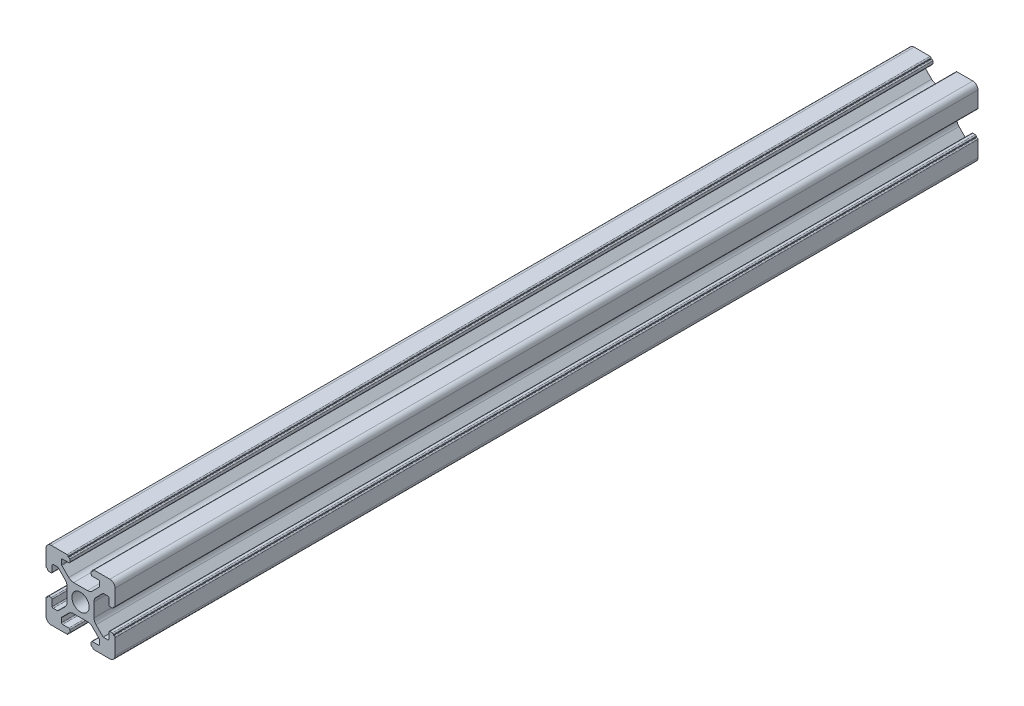
SolidWorks part; units mm, degrees
ref_plane "Front Plane" through (0, 0, 0) normal (0, 0, 1) x (1, 0, 0)
ref_plane "Top Plane" through (0, 0, 0) normal (0, 1, 0) x (1, 0, 0)
ref_plane "Right Plane" through (0, 0, 0) normal (1, 0, 0) x (0, 0, -1)
sketch "Model" plane through (0, 0, 0) normal (0, 0, 1) x (1, 0, 0)
  line L0 (7.8, 0) -> (7.8, -4.0218)
  line L1 (8.9716, -6.8503) -> (13.1213, -11)
  line L2 (13.1213, -11) -> (15.8, -11)
  line L3 (16.4, -10.4) -> (16.4, -6.8)
  line L4 (17, -6.2) -> (18.4, -6.2)
  line L5 (19, -6.8) -> (19, -7.2)
  line L6 (19, -7.2) -> (19.4, -7.2)
  line L7 (20, -7.8) -> (20, -17)
  line L8 (17, -20) -> (7.8, -20)
  line L9 (6.2, -18.4) -> (6.2, -17)
  line L10 (6.8, -16.4) -> (10.4, -16.4)
  line L11 (11, -15.8) -> (11, -13.3698)
  line L12 (10.8243, -12.9456) -> (6.8503, -8.9716)
  line L13 (4.0218, -7.8) -> (0, -7.8)
  line L14 (0, -7.8) -> (-4.0218, -7.8)
  line L15 (-6.8503, -8.9716) -> (-10.8243, -12.9456)
  line L16 (-11, -13.3698) -> (-11, -15.8)
  line L17 (-10.4, -16.4) -> (-6.8, -16.4)
  line L18 (-6.2, -17) -> (-6.2, -18.4)
  line L19 (-7.8, -20) -> (-17, -20)
  line L20 (-20, -17) -> (-20, -7.8)
  line L21 (-19.4, -7.2) -> (-19, -7.2)
  line L22 (-19, -7.2) -> (-19, -6.8)
  line L23 (-18.4, -6.2) -> (-17, -6.2)
  line L24 (-16.4, -6.8) -> (-16.4, -10.4)
  line L25 (-15.8, -11) -> (-13.3698, -11)
  line L26 (-12.9456, -10.8243) -> (-8.9716, -6.8503)
  line L27 (-7.8, -4.0218) -> (-7.8, 0)
  line L28 (-7.8, 0) -> (-7.8, 4.0218)
  line L29 (-8.9716, 6.8503) -> (-12.9456, 10.8243)
  line L30 (-13.3698, 11) -> (-15.8, 11)
  line L31 (-16.4, 10.4) -> (-16.4, 6.8)
  line L32 (-17, 6.2) -> (-18.4, 6.2)
  line L33 (-19, 6.8) -> (-19, 7.2)
  line L34 (-19, 7.2) -> (-19.4, 7.2)
  line L35 (-20, 7.8) -> (-20, 17)
  line L36 (-17, 20) -> (-7.8, 20)
  line L37 (-7.2, 19.4) -> (-7.2, 19)
  line L38 (-7.2, 19) -> (-6.8, 19)
  line L39 (-6.2, 18.4) -> (-6.2, 17)
  line L40 (-6.8, 16.4) -> (-10.4, 16.4)
  line L41 (-11, 15.8) -> (-11, 13.3698)
  line L42 (-10.8243, 12.9456) -> (-6.8503, 8.9716)
  line L43 (-4.0218, 7.8) -> (0, 7.8)
  line L44 (0, 7.8) -> (4.0218, 7.8)
  line L45 (6.8503, 8.9716) -> (10.8243, 12.9456)
  line L46 (11, 13.3698) -> (11, 15.8)
  line L47 (10.4, 16.4) -> (6.8, 16.4)
  line L48 (6.2, 17) -> (6.2, 18.4)
  line L49 (6.8, 19) -> (7.2, 19)
  line L50 (7.2, 19) -> (7.2, 19.4)
  line L51 (7.8, 20) -> (17, 20)
  line L52 (20, 17) -> (20, 7.8)
  line L53 (19.4, 7.2) -> (19, 7.2)
  line L54 (19, 7.2) -> (19, 6.8)
  line L55 (18.4, 6.2) -> (17, 6.2)
  line L56 (16.4, 6.8) -> (16.4, 10.4)
  line L57 (15.8, 11) -> (13.3698, 11)
  line L58 (12.9456, 10.8243) -> (8.9716, 6.8503)
  line L59 (7.8, 4.0218) -> (7.8, 0)
  circle A0 centre (0, 0) radius 5
  arc A1 (7.8, -4.0218) -> (8.9716, -6.8503) centre (11.8, -4.0218) ccw
  arc A2 (15.8, -11) -> (16.4, -10.4) centre (15.8, -10.4) ccw
  arc A3 (17, -6.2) -> (16.4, -6.8) centre (17, -6.8) ccw
  arc A4 (19, -6.8) -> (18.4, -6.2) centre (18.4, -6.8) ccw
  arc A5 (20, -7.8) -> (19.4, -7.2) centre (19.4, -7.8) ccw
  arc A6 (17, -20) -> (20, -17) centre (17, -17) ccw
  arc A7 (7.2, -19.4) -> (7.8, -20) centre (7.8, -19.4) ccw
  arc A8 (7.2, -19.4) -> (6.8, -19) centre (6.8, -19.4) ccw
  arc A9 (6.2, -18.4) -> (6.8, -19) centre (6.8, -18.4) ccw
  arc A10 (6.8, -16.4) -> (6.2, -17) centre (6.8, -17) ccw
  arc A11 (10.4, -16.4) -> (11, -15.8) centre (10.4, -15.8) ccw
  arc A12 (11, -13.3698) -> (10.8243, -12.9456) centre (10.4, -13.3698) ccw
  arc A13 (6.8503, -8.9716) -> (4.0218, -7.8) centre (4.0218, -11.8) ccw
  arc A14 (-4.0218, -7.8) -> (-6.8503, -8.9716) centre (-4.0218, -11.8) ccw
  arc A15 (-10.8243, -12.9456) -> (-11, -13.3698) centre (-10.4, -13.3698) ccw
  arc A16 (-11, -15.8) -> (-10.4, -16.4) centre (-10.4, -15.8) ccw
  arc A17 (-6.2, -17) -> (-6.8, -16.4) centre (-6.8, -17) ccw
  arc A18 (-6.8, -19) -> (-6.2, -18.4) centre (-6.8, -18.4) ccw
  arc A19 (-6.8, -19) -> (-7.2, -19.4) centre (-6.8, -19.4) ccw
  arc A20 (-7.8, -20) -> (-7.2, -19.4) centre (-7.8, -19.4) ccw
  arc A21 (-20, -17) -> (-17, -20) centre (-17, -17) ccw
  arc A22 (-19.4, -7.2) -> (-20, -7.8) centre (-19.4, -7.8) ccw
  arc A23 (-18.4, -6.2) -> (-19, -6.8) centre (-18.4, -6.8) ccw
  arc A24 (-16.4, -6.8) -> (-17, -6.2) centre (-17, -6.8) ccw
  arc A25 (-16.4, -10.4) -> (-15.8, -11) centre (-15.8, -10.4) ccw
  arc A26 (-13.3698, -11) -> (-12.9456, -10.8243) centre (-13.3698, -10.4) ccw
  arc A27 (-8.9716, -6.8503) -> (-7.8, -4.0218) centre (-11.8, -4.0218) ccw
  arc A28 (-7.8, 4.0218) -> (-8.9716, 6.8503) centre (-11.8, 4.0218) ccw
  arc A29 (-12.9456, 10.8243) -> (-13.3698, 11) centre (-13.3698, 10.4) ccw
  arc A30 (-15.8, 11) -> (-16.4, 10.4) centre (-15.8, 10.4) ccw
  arc A31 (-17, 6.2) -> (-16.4, 6.8) centre (-17, 6.8) ccw
  arc A32 (-19, 6.8) -> (-18.4, 6.2) centre (-18.4, 6.8) ccw
  arc A33 (-20, 7.8) -> (-19.4, 7.2) centre (-19.4, 7.8) ccw
  arc A34 (-17, 20) -> (-20, 17) centre (-17, 17) ccw
  arc A35 (-7.2, 19.4) -> (-7.8, 20) centre (-7.8, 19.4) ccw
  arc A36 (-6.2, 18.4) -> (-6.8, 19) centre (-6.8, 18.4) ccw
  arc A37 (-6.8, 16.4) -> (-6.2, 17) centre (-6.8, 17) ccw
  arc A38 (-10.4, 16.4) -> (-11, 15.8) centre (-10.4, 15.8) ccw
  arc A39 (-11, 13.3698) -> (-10.8243, 12.9456) centre (-10.4, 13.3698) ccw
  arc A40 (-6.8503, 8.9716) -> (-4.0218, 7.8) centre (-4.0218, 11.8) ccw
  arc A41 (4.0218, 7.8) -> (6.8503, 8.9716) centre (4.0218, 11.8) ccw
  arc A42 (10.8243, 12.9456) -> (11, 13.3698) centre (10.4, 13.3698) ccw
  arc A43 (11, 15.8) -> (10.4, 16.4) centre (10.4, 15.8) ccw
  arc A44 (6.2, 17) -> (6.8, 16.4) centre (6.8, 17) ccw
  arc A45 (6.8, 19) -> (6.2, 18.4) centre (6.8, 18.4) ccw
  arc A46 (7.8, 20) -> (7.2, 19.4) centre (7.8, 19.4) ccw
  arc A47 (20, 17) -> (17, 20) centre (17, 17) ccw
  arc A48 (19.4, 7.2) -> (20, 7.8) centre (19.4, 7.8) ccw
  arc A49 (18.4, 6.2) -> (19, 6.8) centre (18.4, 6.8) ccw
  arc A50 (16.4, 6.8) -> (17, 6.2) centre (17, 6.8) ccw
  arc A51 (16.4, 10.4) -> (15.8, 11) centre (15.8, 10.4) ccw
  arc A52 (13.3698, 11) -> (12.9456, 10.8243) centre (13.3698, 10.4) ccw
  arc A53 (8.9716, 6.8503) -> (7.8, 4.0218) centre (11.8, 4.0218) ccw
extrude "Boss-Extrude1" add sketch "Model" along normal blind 500
scale "Scale1" bodies to scale 101 scale about centroid uniform scaling yes scale factor 1
